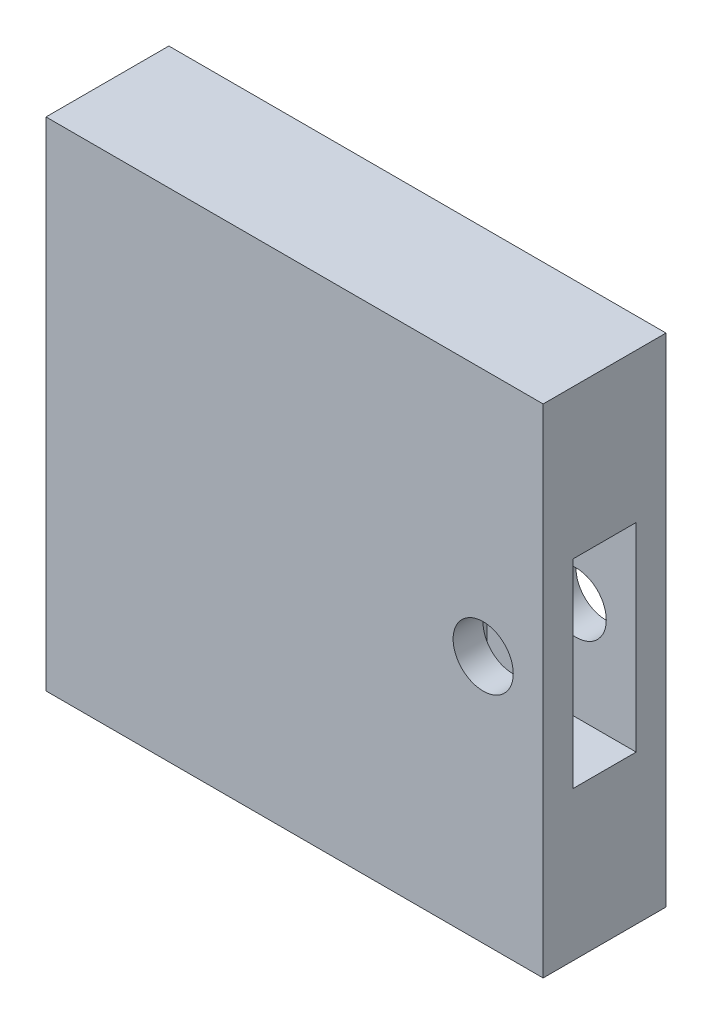
SolidWorks part; units mm, degrees
ref_plane "前视基准面" through (0, 0, 0) normal (0, 0, 1) x (1, 0, 0)
ref_plane "上视基准面" through (0, 0, 0) normal (0, 1, 0) x (1, 0, 0)
ref_plane "右视基准面" through (0, 0, 0) normal (1, 0, 0) x (0, 0, -1)
sketch "草图1" plane through (0, 0, 0) normal (0, 0, 1) x (1, 0, 0)
  line L1 (-25, 25) -> (25, 25)
  line L2 (-25, 25) -> (-25, -25)
  line L3 (-25, -25) -> (25, -25)
  line L4 (25, 25) -> (25, -25)
  dimension "D1" = 25
  dimension "D2" = 25
  dimension "D3" = 25
  dimension "D4" = 25
extrude "凸台-拉伸1" add sketch "草图1" along normal blind 12.3555
sketch "草图2" plane through (0, 0, 12.3555) normal (0, 0, 1) x (1, 0, 0)
  circle A0 centre (18.9691, 0) radius 3.0249
extrude "切除-拉伸1" cut sketch "草图2" against normal blind 15
sketch "草图3" plane through (25, 0, 0) normal (1, 0, 0) x (0, 0, -1)
  line L0 (-12.3555, -25) -> (-12.3555, 25) construction
  line L1 (-9.3555, 10) -> (-3, 10)
  line L2 (-9.3555, 10) -> (-9.3555, -10)
  line L3 (-9.3555, -10) -> (-3, -10)
  line L4 (-3, 10) -> (-3, -10)
  line L5 (0, -25) -> (0, 25) construction
  dimension "D1" = 10
  dimension "D2" = 10
  dimension "D3" = 3
  dimension "D4" = 3
extrude "切除-拉伸2" cut sketch "草图3" against normal blind 15
